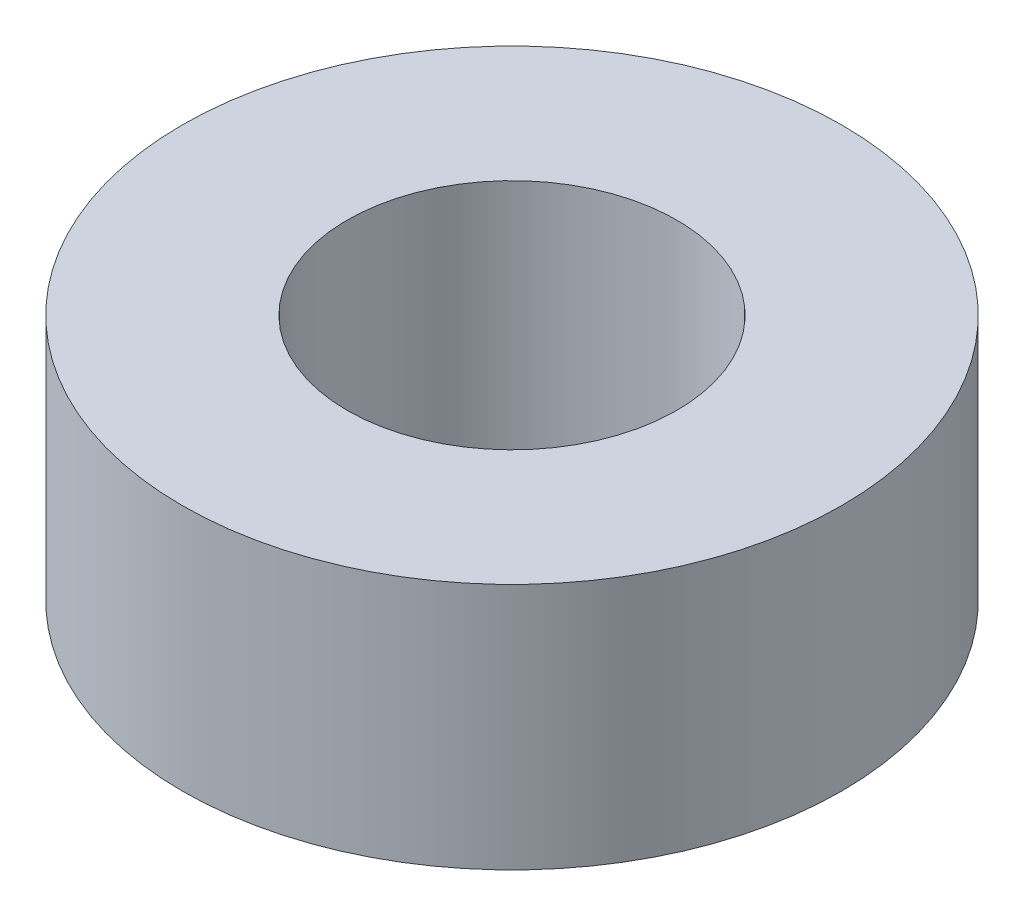
SolidWorks part; units mm, degrees
material "PET"
ref_plane "Front" through (0, 0, 0) normal (0, 0, 1) x (1, 0, 0)
ref_plane "Top" through (0, 0, 0) normal (0, 1, 0) x (1, 0, 0)
ref_plane "Right" through (0, 0, 0) normal (1, 0, 0) x (0, 0, -1)
sketch "Sketch1" plane through (0, 0, 0) normal (0, 1, 0) x (1, 0, 0)
  circle A1 centre (0, 0) radius 3.175
  circle A2 centre (0, 0) radius 6.35
  dimension "D2" = 3.175
  dimension "D1" = 6.35
extrude "Boss-Extrude2" add sketch "Sketch1" along normal blind 4.7625
